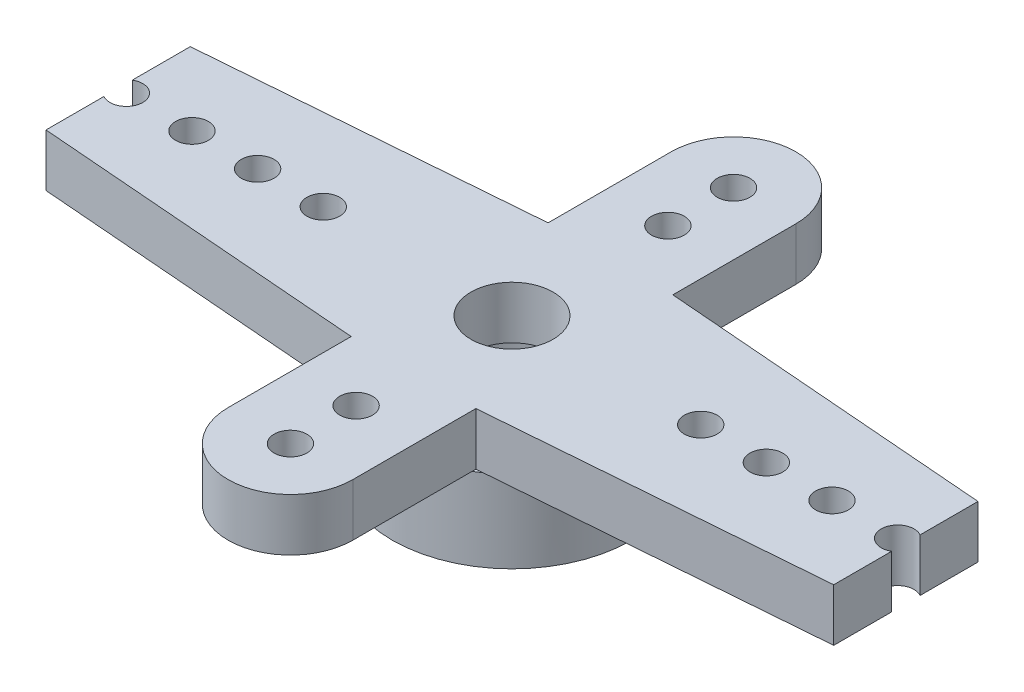
SolidWorks part; units mm, degrees
material "Rubber"
ref_plane "Front Plane" through (0, 0, 0) normal (0, 0, 1) x (1, 0, 0)
ref_plane "Top Plane" through (0, 0, 0) normal (0, 1, 0) x (1, 0, 0)
ref_plane "Right Plane" through (0, 0, 0) normal (1, 0, 0) x (0, 0, -1)
sketch "Sketch1" plane through (0, 0, 0) normal (0, 1, 0) x (1, 0, 0)
  circle A0 centre (0, 0) radius 2.5
  circle A1 centre (0, 0) radius 3.65
  dimension "D1" = 5
  dimension "D2" = 7.3
extrude "Boss-Extrude1" add sketch "Sketch1" along normal blind 2.5
sketch "Sketch2" plane through (0, 2.5, 0) normal (0, 1, 0) x (1, 0, 0)
  line L0 (15.75, 0) -> (-15.75, 0) construction
  line L1 (0, -6.75) -> (0, 6.75) construction
  line L2 (-1.9, 6.75) -> (-1.9, 3)
  line L3 (1.9, 6.75) -> (1.9, 3)
  line L4 (-15.75, 1.9) -> (-1.9, 3)
  line L5 (15.75, 1.9) -> (1.9, 3)
  line L6 (15.75, -1.9) -> (1.9, -3)
  line L7 (1.9, -6.75) -> (1.9, -3)
  line L8 (-1.9, -6.75) -> (-1.9, -3)
  line L9 (-15.75, -1.9) -> (-1.9, -3)
  circle A0 centre (0, 0) radius 1.25
  arc A1 (-1.9, 6.75) -> (1.9, 6.75) centre (0, 6.75) cw
  arc A2 (-15.75, 1.9) -> (-15.75, -1.9) centre (-15.75, 0) ccw
  arc A3 (15.75, 1.9) -> (15.75, -1.9) centre (15.75, 0) cw
  arc A4 (-1.9, -6.75) -> (1.9, -6.75) centre (0, -6.75) ccw
  point P6 (0, 0)
  point P9 (0, 0)
  dimension "D1" = 2.5
  dimension "D4" = 1.9
  dimension "D5" = 1.9
  dimension "D2" = 13.5
  dimension "D3" = 31.5
  dimension "D6" = 1.1
extrude "Boss-Extrude2" add sketch "Sketch2" along normal blind 1.6
sketch "Sketch3" plane through (0, 4.1, 0) normal (0, 1, 0) x (1, 0, 0)
  line L0 (0, -8.65) -> (0, 8.65) construction
  line L1 (-17.65, 0) -> (17.65, 0) construction
  arc A0 (1.9, 6.75) -> (-1.9, 6.75) centre (0, 6.75) ccw construction
  arc A1 (15.75, -1.9) -> (15.75, 1.9) centre (15.75, 0) ccw construction
  circle A2 centre (0, 6.75) radius 0.5
  circle A3 centre (0, 4.75) radius 0.5
  circle A4 centre (-15.75, 0) radius 0.5
  circle A5 centre (-13.75, 0) radius 0.5
  circle A6 centre (-11.75, 0) radius 0.5
  circle A7 centre (-9.75, 0) radius 0.5
  circle A8 centre (-7.75, 0) radius 0.5
  circle A9 centre (-5.75, 0) radius 0.5
  circle A10 centre (5.75, 0) radius 0.5
  circle A11 centre (7.75, 0) radius 0.5
  circle A12 centre (9.75, 0) radius 0.5
  circle A13 centre (11.75, 0) radius 0.5
  circle A14 centre (13.75, 0) radius 0.5
  circle A15 centre (15.75, 0) radius 0.5
  circle A16 centre (0, -4.75) radius 0.5
  circle A17 centre (0, -6.75) radius 0.5
  point P8 (0, 0)
  point P15 (0, 0)
  dimension "D1" = 1
  dimension "D3" = 1
  dimension "D4" = 1
  dimension "D5" = 2
  dimension "D2" = 6
extrude "Cut-Extrude1" cut sketch "Sketch3" against normal up to next
sketch "Sketch4" plane through (0, 4.1, 0) normal (0, 1, 0) x (1, 0, 0)
  line L0 (0, -1000) -> (0, 49000) construction
  line L1 (-20.2853, 6.9234) -> (-12, 6.9234)
  line L2 (-20.2853, 6.9234) -> (-20.2853, -5.0696)
  line L3 (-20.2853, -5.0696) -> (-12, -5.0696)
  line L4 (-12, 6.9234) -> (-12, -5.0696)
  line L5 (20.2853, -5.0696) -> (12, -5.0696)
  line L6 (12, 6.9234) -> (12, -5.0696)
  line L7 (20.2853, 6.9234) -> (12, 6.9234)
  line L8 (20.2853, 6.9234) -> (20.2853, -5.0696)
  dimension "D1" = 12
extrude "Cut-Extrude2" cut sketch "Sketch4" against normal through all
